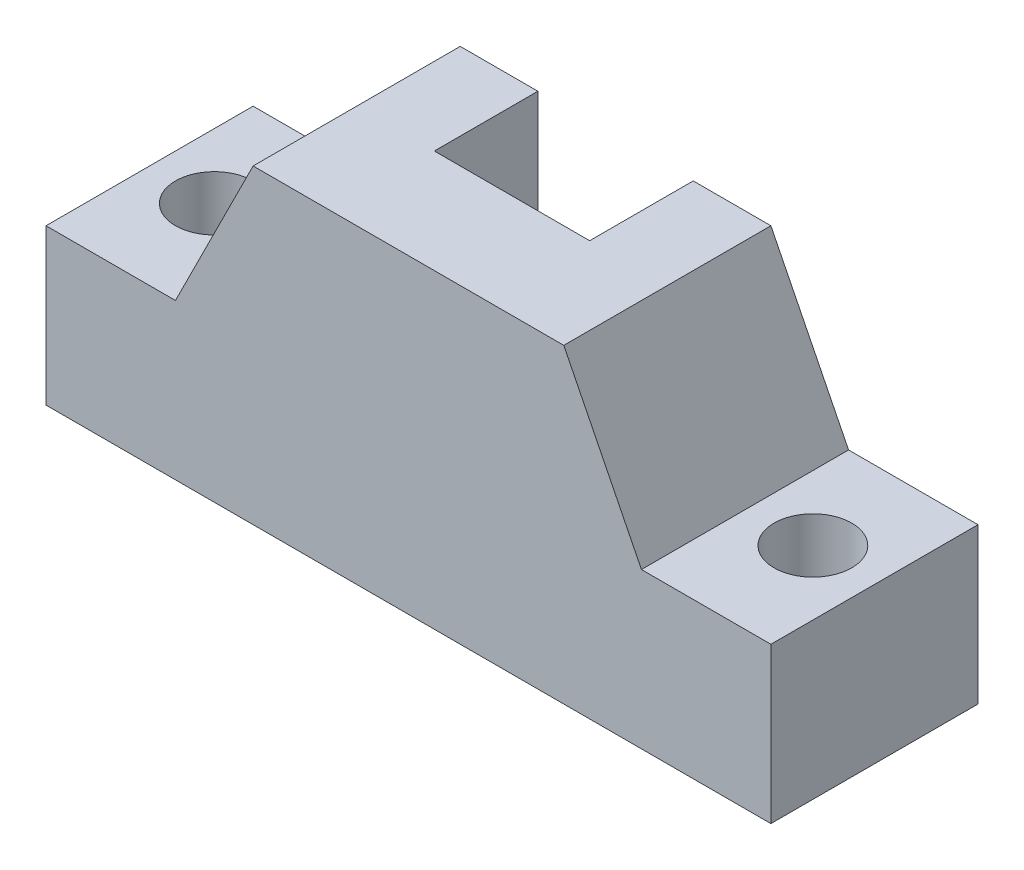
SolidWorks part; units mm, degrees
ref_plane "Alzado" through (0, 0, 0) normal (0, 0, 1) x (1, 0, 0)
ref_plane "Planta" through (0, 0, 0) normal (0, 1, 0) x (1, 0, 0)
ref_plane "Vista lateral" through (0, 0, 0) normal (1, 0, 0) x (0, 0, -1)
sketch "Croquis1" plane through (0, 0, 0) normal (0, 0, 1) x (1, 0, 0)
  line L0 (0, 0) -> (140, 0)
  line L1 (140, 0) -> (140, 30)
  line L2 (140, 30) -> (115, 30)
  line L3 (70, 0) -> (70, 60) construction
  line L4 (40, 60) -> (100, 60)
  line L5 (100, 60) -> (115, 30)
  line L6 (0, 0) -> (0, 30)
  line L7 (0, 30) -> (25, 30)
  line L8 (40, 60) -> (25, 30)
  dimension "D1" = 15
  dimension "D2" = 60
  dimension "D3" = 25
  dimension "D4" = 30
extrude "Saliente-Extruir1" add sketch "Croquis1" along normal blind 40
sketch "Croquis2" plane through (0, 30, 0) normal (0, 1, 0) x (1, 0, 0)
  circle A0 centre (127.5324, -19.4219) radius 7.5
extrude "Cortar-Extruir1" cut sketch "Croquis2" against normal blind 40
sketch "Croquis3" plane through (0, 30, 0) normal (0, 1, 0) x (1, 0, 0)
  circle A0 centre (12.5, -20) radius 7.5
extrude "Cortar-Extruir2" cut sketch "Croquis3" against normal blind 40
sketch "Croquis15" plane through (0, 60, 0) normal (0, 1, 0) x (1, 0, 0)
  line L0 (70, 0) -> (70, -40) construction
  line L1 (100, 0) -> (40, 0) construction
  line L2 (100, -40) -> (40, -40) construction
ref_plane "Plano3" through (70, 0, 0) normal (1, 0, 0) x (0, 0, -1)
sketch "Croquis16" plane through (70, 0, 0) normal (1, 0, 0) x (0, 0, -1)
  line L0 (0, 60) -> (-20, 60)
  line L1 (0, 60) -> (0, 25.359)
  line L2 (0, 60) -> (-40, 60) construction
  line L3 (-20, 60) -> (0, 25.359)
  dimension "D1" = 60
extrude "Cortar-Extruir4" cut sketch "Croquis16" against normal blind 15 and the other way blind 15
ref_plane "Plano1" through (70, 0, 0) normal (1, 0, 0) x (0, 0, -1)
sketch "Croquis9" plane through (70, 0, 0) normal (1, 0, 0) x (0, 0, -1)
  line L0 (-20, 60) -> (-40, 25.359)
  line L1 (-40, 60) -> (-40, 0) construction
  line L2 (-40, 60) -> (-20, 60) construction
  line L3 (-40, 60) -> (-40, 25.359)
  dimension "D1" = 60
